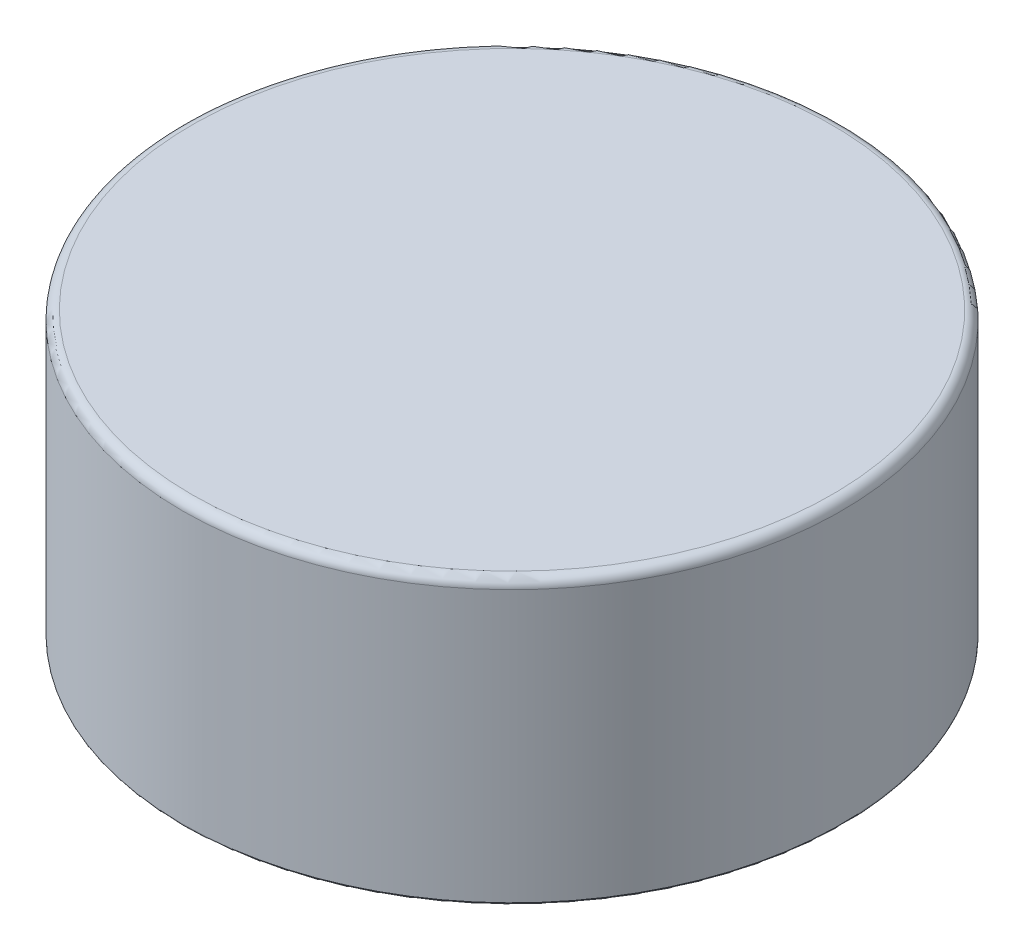
SolidWorks part; units mm, degrees
ref_plane "Front Plane" through (0, 0, 0) normal (0, 0, 1) x (1, 0, 0)
ref_plane "Top Plane" through (0, 0, 0) normal (0, 1, 0) x (1, 0, 0)
ref_plane "Right Plane" through (0, 0, 0) normal (1, 0, 0) x (0, 0, -1)
sketch "Sketch1" plane through (0, 0, 0) normal (0, 1, 0) x (1, 0, 0)
  circle A0 centre (0, 0) radius 35
extrude "Boss-Extrude1" add sketch "Sketch1" along normal blind 30
sketch "Sketch2" plane through (0, 0, 0) normal (0, 1, 0) x (1, 0, 0)
  circle A0 centre (0, 0) radius 34.3
extrude "Cut-Extrude1" cut sketch "Sketch2" along normal blind 25
fillet "Fillet1" radius 1 1 edges at (0, 30, 35)
fillet "Fillet2" radius 0.2 1 edges at (0, 0, 35)
